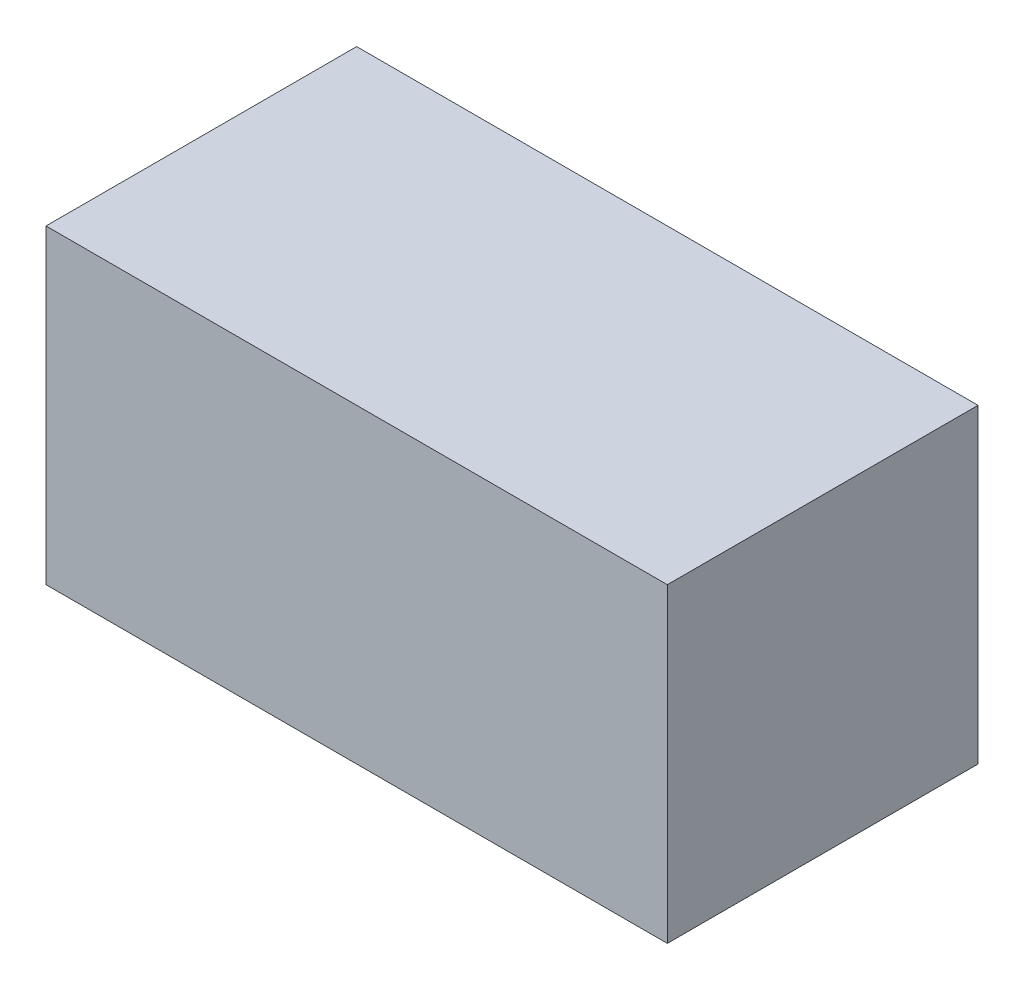
SolidWorks part; units mm, degrees
material "AISI 304"
ref_plane "Front Plane" through (0, 0, 0) normal (0, 0, 1) x (1, 0, 0)
ref_plane "Top Plane" through (0, 0, 0) normal (0, 1, 0) x (1, 0, 0)
ref_plane "Right Plane" through (0, 0, 0) normal (1, 0, 0) x (0, 0, -1)
sketch "Sketch1" plane through (0, 0, 0) normal (0, 1, 0) x (1, 0, 0)
  line L1 (-25.4, -12.7) -> (25.4, -12.7)
  line L2 (-25.4, -12.7) -> (-25.4, 12.7)
  line L3 (-25.4, 12.7) -> (25.4, 12.7)
  line L4 (25.4, -12.7) -> (25.4, 12.7)
  line L5 (-25.4, -12.7) -> (25.4, 12.7) construction
  line L6 (-25.4, 12.7) -> (25.4, -12.7) construction
  point P0 (0, 0)
  dimension "D1" = 25.4
  dimension "D2" = 50.8
extrude "Boss-Extrude1" add sketch "Sketch1" along normal blind 25.4
hole_wizard "Pipe Tap Drill for 1/2 Tap1" positions "Sketch2" profile "Sketch4" hole size "1/2" standard "ANSI Inch"
sketch "Sketch2" plane through (-25.4, 0, 0) normal (-1, 0, 0) x (0, 0, 1)
  line L0 (0, 0) -> (0, 25.4) construction
  line L1 (-12.7, 25.4) -> (12.7, 25.4) construction
  point P0 (0, 12.7)
  point P11 (0, 12.7)
sketch "Sketch4" plane through (-25.4, 12.7, 0) normal (0, 1, 0) x (0, 0, 1)
  line L0 (0, 0) -> (0, 43.4645)
  line L1 (0, 43.4645) -> (8.9281, 38.1)
  line L2 (8.9281, 38.1) -> (8.9281, 0)
  line L5 (8.9281, 0) -> (0, 0)
  line L10 (0, 43.4645) -> (-8.9281, 38.1) construction
  line L11 (0, -6.35) -> (0, 107.95) construction
  dimension "Hole Dia." = 17.8562
  dimension "Hole Depth" = 38.1
  dimension "Drill Angle" = 118
sketch "Sketch5" plane through (0, 0, 0) normal (0, 0, 1) x (1, 0, 0)
  line L0 (-9.3522, -14.1147) -> (11.9544, 7.1919)
  line L1 (-12.7, -10.7669) -> (-6.0044, -17.4625)
  line L2 (-6.0044, -17.4625) -> (0.8419, -5.6044)
  line L3 (0.8419, -5.6044) -> (12.7963, 6.35)
  line L4 (12.7963, 6.35) -> (11.1125, 8.0338)
  line L5 (11.1125, 8.0338) -> (-0.8419, -3.9206)
  line L6 (-0.8419, -3.9206) -> (-12.7, -10.7669)
  line L7 (0, 0) -> (0, -4.7625) construction
  line L8 (-0.8419, -3.9206) -> (0.8419, -5.6044) construction
  point P4 (-9.3522, -14.1147)
  point P12 (11.9544, 7.1919)
  point P13 (0, -4.7625)
  point P14 (19.7995, 14.3838)
  point P15 (-8.1073, -9.7591)
  point P16 (22.8006, 14.3838)
  point P17 (-10.3016, -9.3822)
  dimension "D1" = 15
  dimension "D2" = 45
  dimension "D3" = 2.3813
  dimension "D4" = 6.35
  dimension "D5" = 4.7625
  dimension "D6" = 12.7
revolve "Cut-Revolve2" cut sketch "Sketch5" angle 360 about L0
